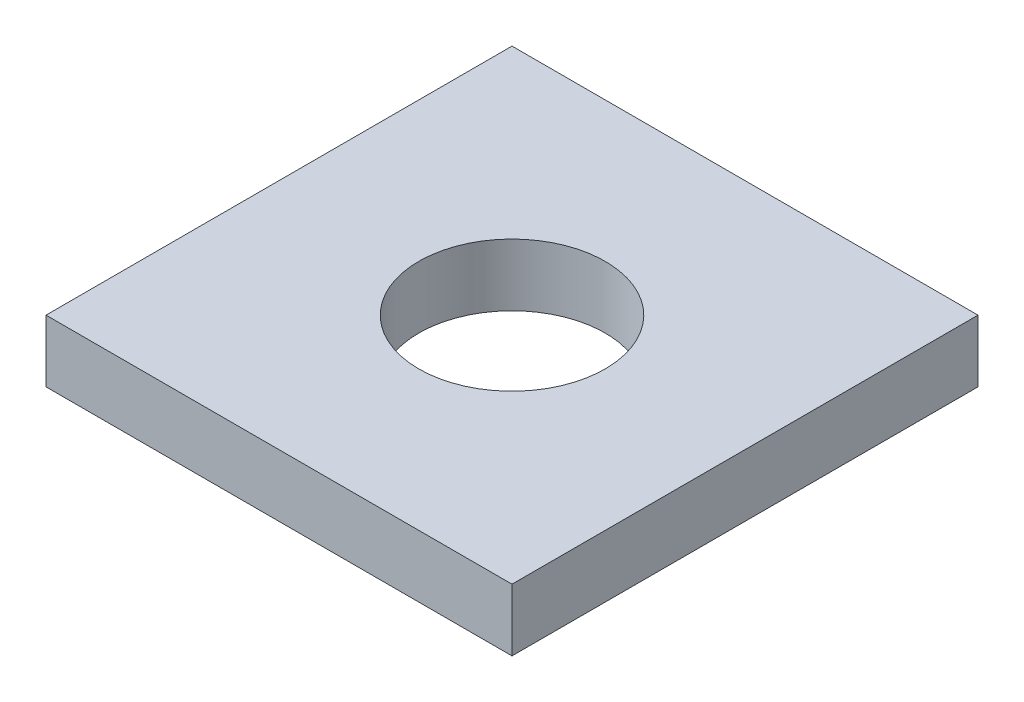
SolidWorks part; units mm, degrees
ref_plane "Front Plane" through (0, 0, 0) normal (0, 0, 1) x (1, 0, 0)
ref_plane "Top Plane" through (0, 0, 0) normal (0, 1, 0) x (1, 0, 0)
ref_plane "Right Plane" through (0, 0, 0) normal (1, 0, 0) x (0, 0, -1)
sketch "Sketch1" plane through (0, 0, 0) normal (0, 1, 0) x (1, 0, 0)
  line L1 (3.81, 3.81) -> (-3.81, 3.81)
  line L2 (3.81, 3.81) -> (3.81, -3.81)
  line L3 (3.81, -3.81) -> (-3.81, -3.81)
  line L4 (-3.81, 3.81) -> (-3.81, -3.81)
  line L5 (3.81, 3.81) -> (-3.81, -3.81) construction
  line L6 (3.81, -3.81) -> (-3.81, 3.81) construction
  circle A0 centre (0, 0) radius 1.524
  point P0 (0, 0)
  dimension "D1" = 7.62
  dimension "D2" = 7.62
extrude "Boss-Extrude1" add sketch "Sketch1" along normal blind 1.016
